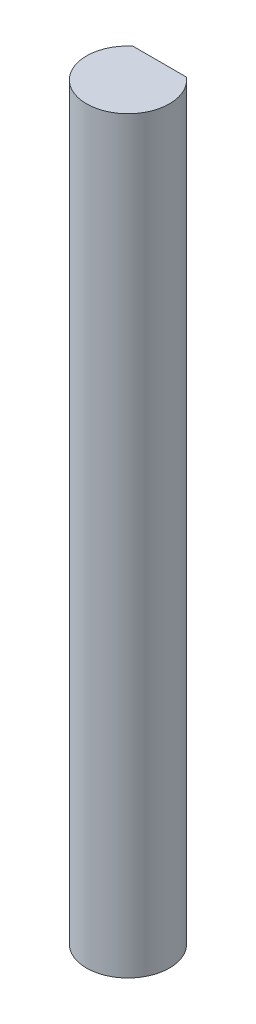
SolidWorks part; units mm, degrees
material "AISI 304"
ref_plane "Front Plane" through (0, 0, 0) normal (0, 0, 1) x (1, 0, 0)
ref_plane "Top Plane" through (0, 0, 0) normal (0, 1, 0) x (1, 0, 0)
ref_plane "Right Plane" through (0, 0, 0) normal (1, 0, 0) x (0, 0, -1)
sketch "Sketch1" plane through (0, 0, 0) normal (0, 1, 0) x (1, 0, 0)
  line L0 (-2.0492, 2.4168) -> (2.0492, 2.4168)
  arc A0 (-2.0492, 2.4168) -> (2.0492, 2.4168) centre (0, 0) ccw
  point P3 (0, -3.1686)
  dimension "D1" = 6.3373
  dimension "D2" = 5.5855
extrude "Boss-Extrude1" add sketch "Sketch1" along normal mid plane 57.15
